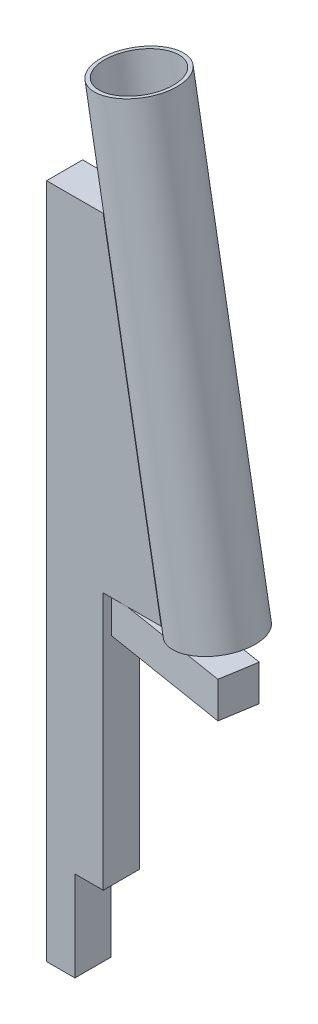
SolidWorks part; units mm, degrees
ref_plane "Front Plane" through (0, 0, 0) normal (0, 0, 1) x (1, 0, 0)
ref_plane "Top Plane" through (0, 0, 0) normal (0, 1, 0) x (1, 0, 0)
ref_plane "Right Plane" through (0, 0, 0) normal (1, 0, 0) x (0, 0, -1)
sketch "Esquisse1" plane through (0, 0, 0) normal (0, 0, 1) x (1, 0, 0)
  line L0 (0, 525.2077) -> (0, 0)
  line L1 (0, 0) -> (22, 0)
  line L2 (22, 0) -> (22, 70)
  line L3 (22, 70) -> (44, 70)
  line L4 (44, 70) -> (44, 270)
  line L5 (44, 270) -> (89, 270)
  line L6 (89, 270) -> (44, 525.2077)
  line L7 (44, 525.2077) -> (0, 525.2077)
  dimension "D1" = 100
  dimension "D2" = 22
  dimension "D3" = 45
  dimension "D4" = 70
  dimension "D5" = 22
  dimension "D6" = 270
extrude "Main Extrusion" add sketch "Esquisse1" along normal mid plane 28
sketch "Esquisse2" plane through (0, 270, 0) normal (0, -1, 0) x (-1, 0, 0)
  line L0 (-61.7505, -13.8181) -> (-66.2495, 13.8181) construction
  line L1 (-47.9324, -11.5686) -> (-146.6332, -27.6362)
  line L2 (-47.9324, -11.5686) -> (-52.4314, 16.0676)
  line L3 (-52.4314, 16.0676) -> (-151.1321, 0)
  line L4 (-146.6332, -27.6362) -> (-151.1321, 0)
  line L5 (-148.8826, -13.8181) -> (-50.1819, 2.2495) construction
  line L9 (-44, -14) -> (-44, 14) construction
  point P8 (-64, 0)
  point P11 (-44, 0)
  dimension "D1" = 28
  dimension "D2" = 100
  dimension "D3" = 86
  dimension "D4" = 20
extrude "Lock Extrusion" add sketch "Esquisse2" along normal blind 28
ref_plane "Plan3" through (-43.489, 246.6386, 0) normal (0.1736, -0.9848, 0) x (0, 0, -1)
sketch "Esquisse3" plane through (-43.489, 246.6386, 0) normal (0.1736, -0.9848, 0) x (0, 0, -1)
  line L2 (-14, 134.5329) -> (14, 134.5329) construction
  line L3 (0, 48.95) -> (0, -48.95) construction
  circle A0 centre (0, 164.5329) radius 27
  circle A1 centre (0, 164.5329) radius 30
  dimension "D1" = 60
  dimension "D2" = 54
extrude "Plexiglas" add sketch "Esquisse3" against normal blind 350 separate body
